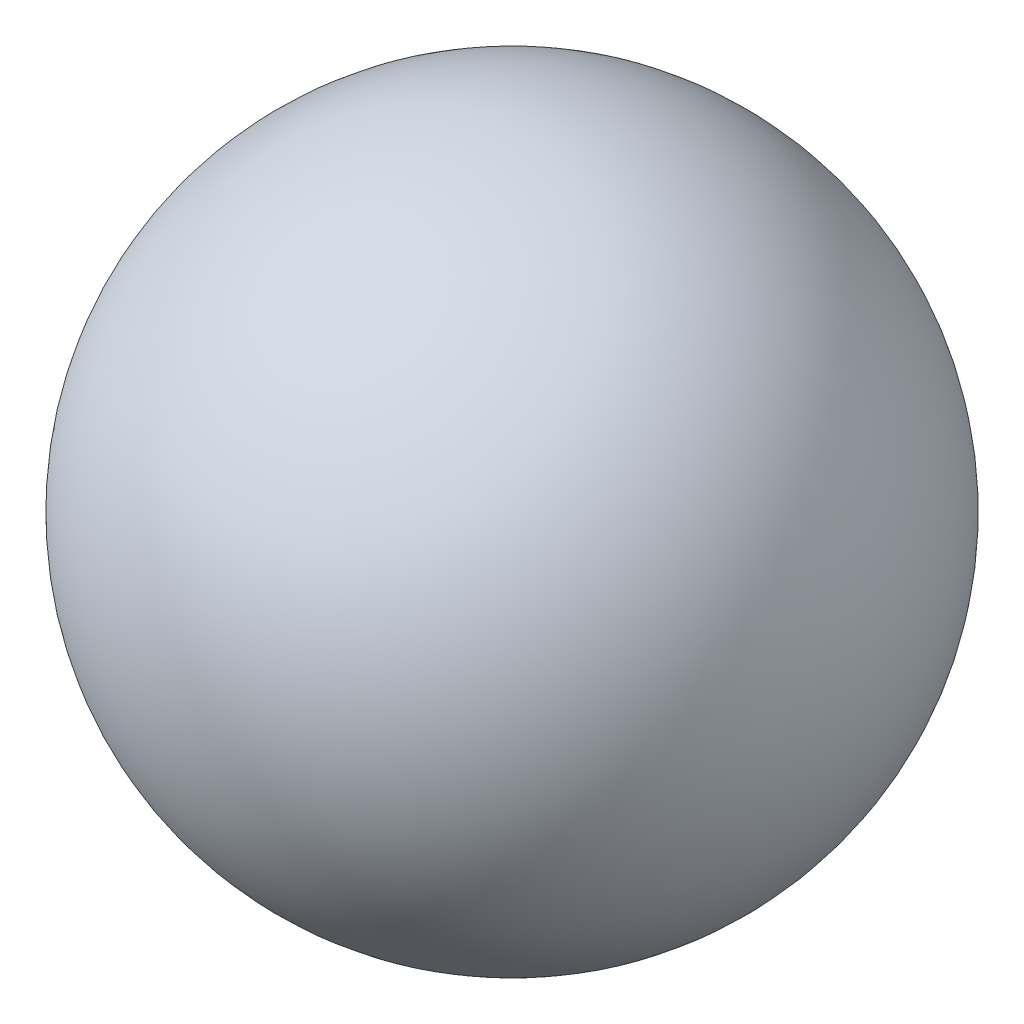
SolidWorks part; units mm, degrees
ref_plane "Front Plane" through (0, 0, 0) normal (0, 0, 1) x (1, 0, 0)
ref_plane "Top Plane" through (0, 0, 0) normal (0, 1, 0) x (1, 0, 0)
ref_plane "Right Plane" through (0, 0, 0) normal (1, 0, 0) x (0, 0, -1)
sketch "Sketch1" plane through (0, 0, 0) normal (0, 0, 1) x (1, 0, 0)
  line L1 (0, 109.15) -> (0, -109.15)
  arc A0 (0, 109.15) -> (0, -109.15) centre (0, 0) ccw
  dimension "D1" = 218.3
revolve "Revolve5" add sketch "Sketch1" angle 360 about L1
